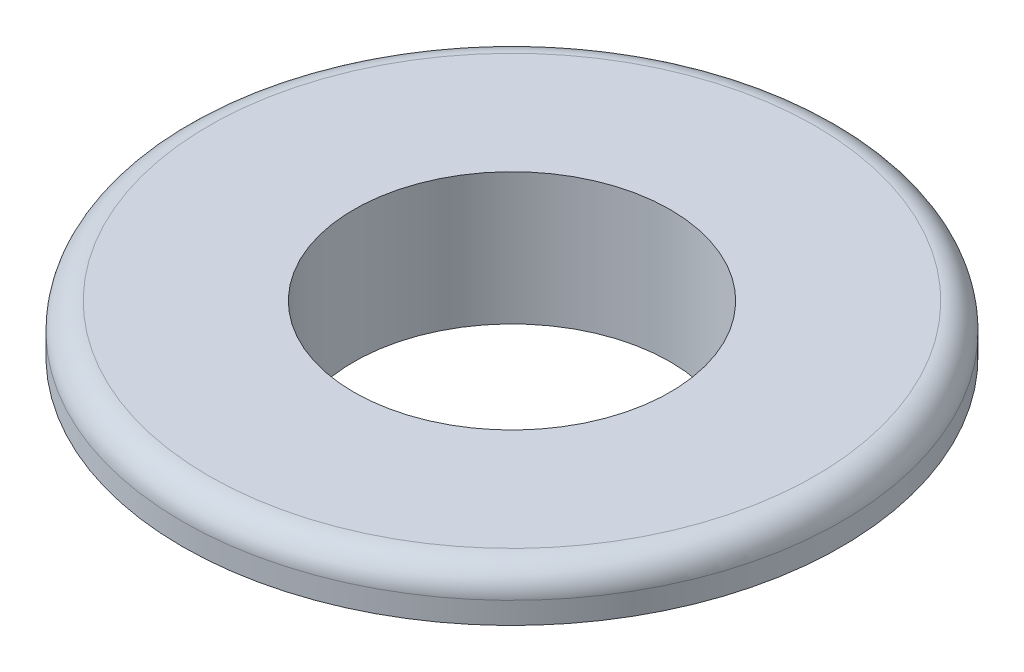
SolidWorks part; units mm, degrees
ref_plane "Front Plane" through (0, 0, 0) normal (0, 0, 1) x (1, 0, 0)
ref_plane "Top Plane" through (0, 0, 0) normal (0, 1, 0) x (1, 0, 0)
ref_plane "Right Plane" through (0, 0, 0) normal (1, 0, 0) x (0, 0, -1)
sketch "Sketch1" plane through (0, 0, 0) normal (0, 1, 0) x (1, 0, 0)
  circle A0 centre (0, 0) radius 6
  circle A1 centre (0, 0) radius 7
  dimension "D1" = 12
  dimension "D2" = 14
extrude "Boss-Extrude1" add sketch "Sketch1" along normal blind 3.175
sketch "Sketch2" plane through (0, 3.175, 0) normal (0, 1, 0) x (1, 0, 0)
  circle A0 centre (0, 0) radius 12.5
  circle A1 centre (0, 0) radius 6 construction
  circle A2 centre (0, 0) radius 6
  dimension "D1" = 25
extrude "Boss-Extrude2" add sketch "Sketch2" along normal blind 1.825
fillet "Fillet1" radius 1 1 edges at (0, 5, 12.5)
